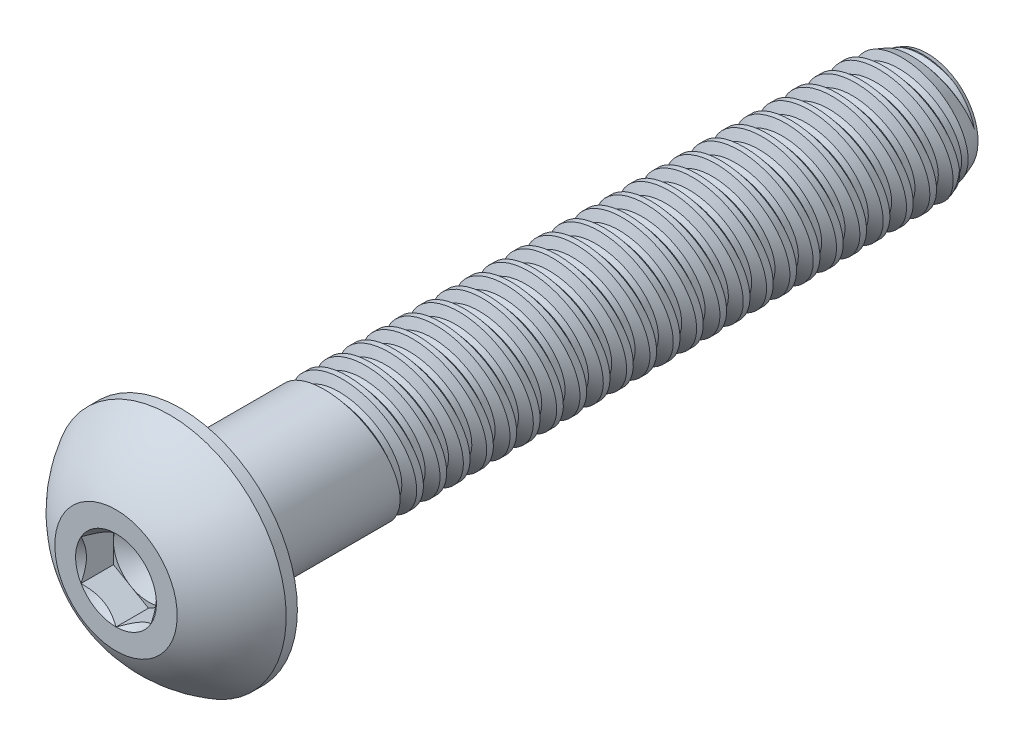
SolidWorks part; units mm, degrees
ref_plane "Front" through (0, 0, 0) normal (0, 0, 1) x (1, 0, 0)
ref_plane "Top" through (0, 0, 0) normal (0, 1, 0) x (1, 0, 0)
ref_plane "Right" through (0, 0, 0) normal (1, 0, 0) x (0, 0, -1)
sketch "Sketch1" plane through (0, 0, 0) normal (1, 0, 0) x (0, 0, -1)
  line L0 (0, 0) -> (-2.2098, 0) construction
  line L1 (0, 0) -> (25.4, 0)
  line L2 (0, 0) -> (0, 2.0828)
  line L3 (0, 2.0828) -> (25.4, 2.0828)
  line L4 (25.4, 0) -> (25.4, 2.0828)
  line L5 (0, -2.0828) -> (25.4, -2.0828) construction
  dimension "Thread Dia" = 4.1656
  dimension "Length" = 25.4
  dimension "Head Height" = 2.2098
revolve "Revolve1" add sketch "Sketch1" angle 360 about L0
ref_plane "Plane1" through (0, 0, 2.2098) normal (0, 0, 1) x (1, 0, 0)
sketch "Sketch2" plane through (0, 0, 0) normal (1, 0, 0) x (0, 0, -1)
  line L0 (4.7625, 2.0828) -> (4.7625, -2.0828) construction
  line L1 (4.7625, -2.0828) -> (5.5563, -2.0828) construction
  line L2 (5.5563, -2.0828) -> (4.7625, 2.0828) construction
  line L3 (4.7625, 2.0828) -> (4.86, 2.1014) construction
  line L4 (4.86, 2.1014) -> (5.5422, 2.2314)
  line L5 (5.5422, 2.2314) -> (5.379, 1.7629)
  line L6 (5.379, 1.7629) -> (5.184, 1.7258)
  line L7 (5.184, 1.7258) -> (4.86, 2.1014)
  line L8 (5.2815, 1.7443) -> (5.2011, 2.1664) construction
  line L9 (0, -2.0828) -> (25.4, -2.0828) construction
  line L10 (0, 2.0828) -> (25.4, 2.0828) construction
  line L11 (25.4, 0) -> (25.4, 2.0828) construction
  line L12 (5.217, 2.0828) -> (6.0108, -2.0828) construction
  line L13 (4.7625, -0.1622) -> (6.4653, 0.1622) construction
  line L14 (-273.05, 2.0828) -> (-273.05, -2.0828) construction
  point P19 (5.6139, 0)
  dimension "D1" = 60
  dimension "Thread Pitch" = 0.7937
  dimension "D2" = 0.0992
  dimension "D3" = 0.1984
  dimension "D4" = 0.7937
  dimension "Thread Length" = 298.45
  dimension "Min Thread Length" = 20.6375
revolve "Cut-Revolve1" cut sketch "Sketch2" angle 360 about L13
sketch "Sketch3" plane through (0, 0, 0) normal (1, 0, 0) x (0, 0, -1)
  line L0 (25.4, 1.7258) -> (24.4191, 2.0828)
  line L1 (24.4191, 2.0828) -> (25.4, 2.0828)
  line L2 (25.4, 2.0828) -> (25.4, 1.7258)
  line L3 (0, 2.0828) -> (25.4, 2.0828) construction
  line L4 (25.4, 0) -> (25.4, 2.0828) construction
  line L5 (24.4191, 0) -> (0, 0) construction
  line L6 (24.4191, 2.0828) -> (24.4191, -2.0828) construction
  line L7 (0, -2.0828) -> (25.4, -2.0828) construction
  dimension "D1" = 20
  dimension "D2" = 4.1656
revolve "Cut-Revolve2" cut sketch "Sketch3" angle 360 about L5
pattern_linear "LPattern1" count 26 spacing 0.7937 along (0, 0, 1)
sketch "Sketch4" plane through (0, 0, 0) normal (0, 0, 1) x (1, 0, 0)
  circle A0 centre (0, 0) radius 3.9624
  dimension "Head Dia" = 7.9248
extrude "Extrude1" add sketch "Sketch4" along normal up to surface (2.2098 mm away)
sketch "Sketch9" plane through (0, 0, 0) normal (1, 0, 0) x (0, 0, -1)
  line L0 (0, 3.9624) -> (-0.381, 3.9624)
  line L1 (-2.2098, 2.0828) -> (-2.5908, 2.0828)
  line L2 (-2.5908, 2.0828) -> (-2.5908, 4.3434)
  line L3 (0, 0) -> (-2.2098, 0) construction
  line L4 (-2.5908, 4.3434) -> (0, 4.3434)
  line L5 (0, 4.3434) -> (0, 3.9624)
  line L10 (0, 0) -> (0, 2.0828) construction
  line L11 (0, 3.9624) -> (-2.2098, 3.9624) construction
  line L12 (0, 2.0828) -> (25.4, 2.0828) construction
  line L13 (-2.2098, 3.9624) -> (-2.2098, -3.9624) construction
  arc A0 (-0.381, 3.9624) -> (-2.2098, 2.0828) centre (1.8112, 0) ccw
  dimension "Side Head Height" = 0.381
revolve "Cut-Revolve3" cut sketch "Sketch9" angle 360 about L3
sketch "Sketch6" plane through (0, 0, 2.2098) normal (0, 0, 1) x (1, 0, 0)
  line L1 (0, -1.3748) -> (1.1906, -0.6874)
  line L2 (1.1906, -0.6874) -> (1.1906, 0.6874)
  line L3 (1.1906, 0.6874) -> (0, 1.3748)
  line L4 (0, 1.3748) -> (-1.1906, 0.6874)
  line L5 (-1.1906, 0.6874) -> (-1.1906, -0.6874)
  line L6 (-1.1906, -0.6874) -> (0, -1.3748)
  circle A0 centre (0, 0) radius 1.1906 construction
  dimension "Hex" = 2.3813
extrude "Cut-Extrude1" cut sketch "Sketch6" against normal blind 1.1049
sketch "Sketch7" plane through (0, 0, 2.2098) normal (0, 0, 1) x (1, 0, 0)
  circle A0 centre (0, 0) radius 1.3748
extrude "Cut-Extrude4" cut sketch "Sketch7" against normal blind 1.1049 draft 45
sketch "Sketch8" plane through (0, 0, 1.1049) normal (0, 0, 1) x (1, 0, 0)
  circle A0 centre (0, 0) radius 1.1906 construction
  circle A1 centre (0, 0) radius 1.1906
extrude "Cut-Extrude5" cut sketch "Sketch8" against normal blind 0.3683 draft 60
equation "\"D2@Sketch2\"=\"Thread Pitch@Sketch2\"/8"
equation "\"D3@Sketch2\"=\"Thread Pitch@Sketch2\"/4"
equation "\"D4@Sketch2\"=\"Thread Pitch@Sketch2\""
equation "\"D3@LPattern1\"=\"Thread Pitch@Sketch2\""
equation "\"D1@LPattern1\"=\"Min Thread Length@Sketch2\"/\"Thread Pitch@Sketch2\""
equation "\"D1@Cut-Extrude1\"=\"Head Height@Sketch1\"/2"
equation "\"D1@Cut-Extrude4\"=\"D1@Cut-Extrude1\""
equation "\"D1@Cut-Extrude5\"=\"D1@Cut-Extrude1\"/3"
